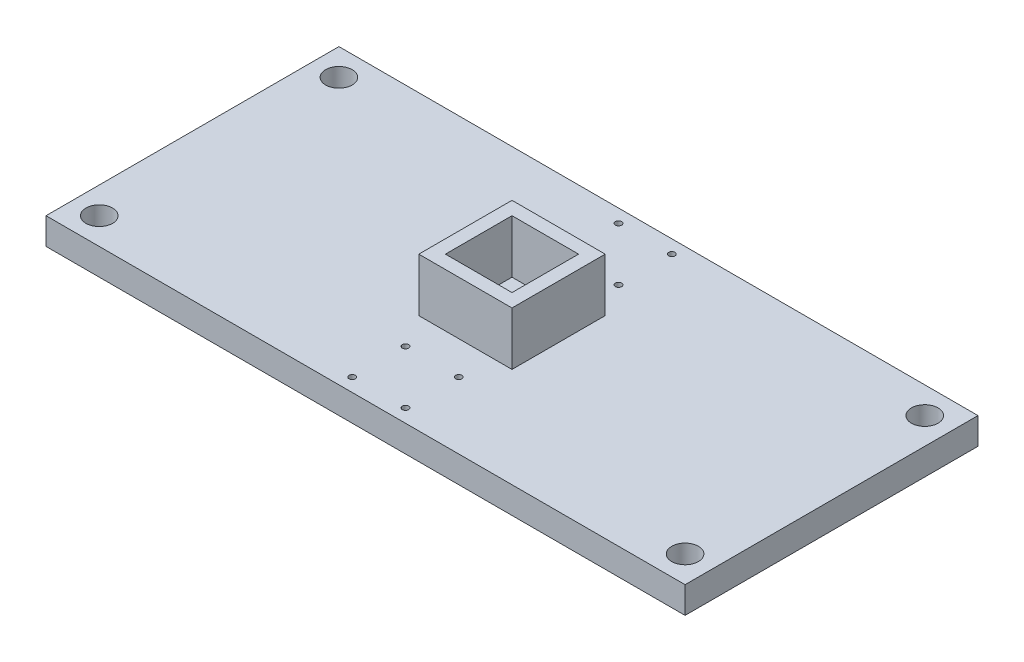
SolidWorks part; units mm, degrees
ref_plane "Front Plane" through (0, 0, 0) normal (0, 0, 1) x (1, 0, 0)
ref_plane "Top Plane" through (0, 0, 0) normal (0, 1, 0) x (1, 0, 0)
ref_plane "Right Plane" through (0, 0, 0) normal (1, 0, 0) x (0, 0, -1)
sketch "Sketch1" plane through (0, 0, 0) normal (0, 1, 0) x (1, 0, 0)
  line L1 (0, 0) -> (304.8, 0)
  line L2 (0, 0) -> (0, 139.7)
  line L3 (0, 139.7) -> (304.8, 139.7)
  line L4 (304.8, 0) -> (304.8, 139.7)
  dimension "D1" = 139.7
  dimension "D2" = 304.8
extrude "Boss-Extrude1" add sketch "Sketch1" along normal blind 12.7
sketch "Sketch5" plane through (0, 12.7, 0) normal (0, 1, 0) x (1, 0, 0)
  line L0 (0, 0) -> (304.8, 0) construction
  line L1 (152.4, 139.7) -> (152.4, 0) construction
  line L2 (304.8, 139.7) -> (0, 139.7) construction
  line L3 (0, 69.85) -> (152.4, 69.85) construction
  line L4 (0, 139.7) -> (0, 0) construction
  circle A1 centre (165.1, 6.35) radius 1.5
  circle A2 centre (165.1, 31.75) radius 1.5
  circle A3 centre (139.7, 31.75) radius 1.5
  circle A16 centre (12.7, 12.7) radius 6.35
  circle A20 centre (139.7, 6.35) radius 1.5
  circle A21 centre (292.1, 12.7) radius 6.35
  point P12 (152.4, 0)
  point P38 (152.4, 69.85)
  dimension "D5" = 3
  dimension "D6" = 3
  dimension "D7" = 3
  dimension "D8" = 25.4
  dimension "D12" = 12.7
  dimension "D2" = 3
  dimension "D1" = 25.4
  dimension "D3" = 90
  dimension "D4" = 25.4
  dimension "D9" = 6.35
  dimension "D10" = 12.7
  dimension "D13" = 12.7
  dimension "D14" = 12.7
  dimension "D16" = 12.7
  dimension "D11" = 25.4
extrude "Cut-Extrude2" cut sketch "Sketch5" against normal through all
sketch "Sketch8" plane through (0, 12.7, 0) normal (0, 1, 0) x (1, 0, 0)
  line L0 (304.8, 0) -> (304.8, 139.7) construction
  line L1 (136.525, 53.975) -> (168.275, 53.975)
  line L2 (136.525, 53.975) -> (136.525, 85.725)
  line L3 (136.525, 85.725) -> (168.275, 85.725)
  line L4 (168.275, 53.975) -> (168.275, 85.725)
  line L5 (304.8, 139.7) -> (0, 139.7) construction
  line L6 (130.175, 47.625) -> (174.625, 47.625)
  line L7 (174.625, 47.625) -> (174.625, 92.075)
  line L8 (130.175, 92.075) -> (174.625, 92.075)
  line L9 (130.175, 47.625) -> (130.175, 92.075)
  point P4 (152.4, 85.725)
  point P7 (168.275, 69.85)
  dimension "D1" = 31.75
  dimension "D2" = 31.75
  dimension "D3" = 152.4
  dimension "D4" = 69.85
  dimension "D5" = 6.35
extrude "Boss-Extrude3" add sketch "Sketch8" along normal blind 25.4
ref_plane "Plane1" through (0, 0, -69.85) normal (0, 0, 1) x (1, 0, 0)
mirror "Mirror1" about plane through (0, 0, -69.85) normal (0, 0, 1) of "Cut-Extrude2"
